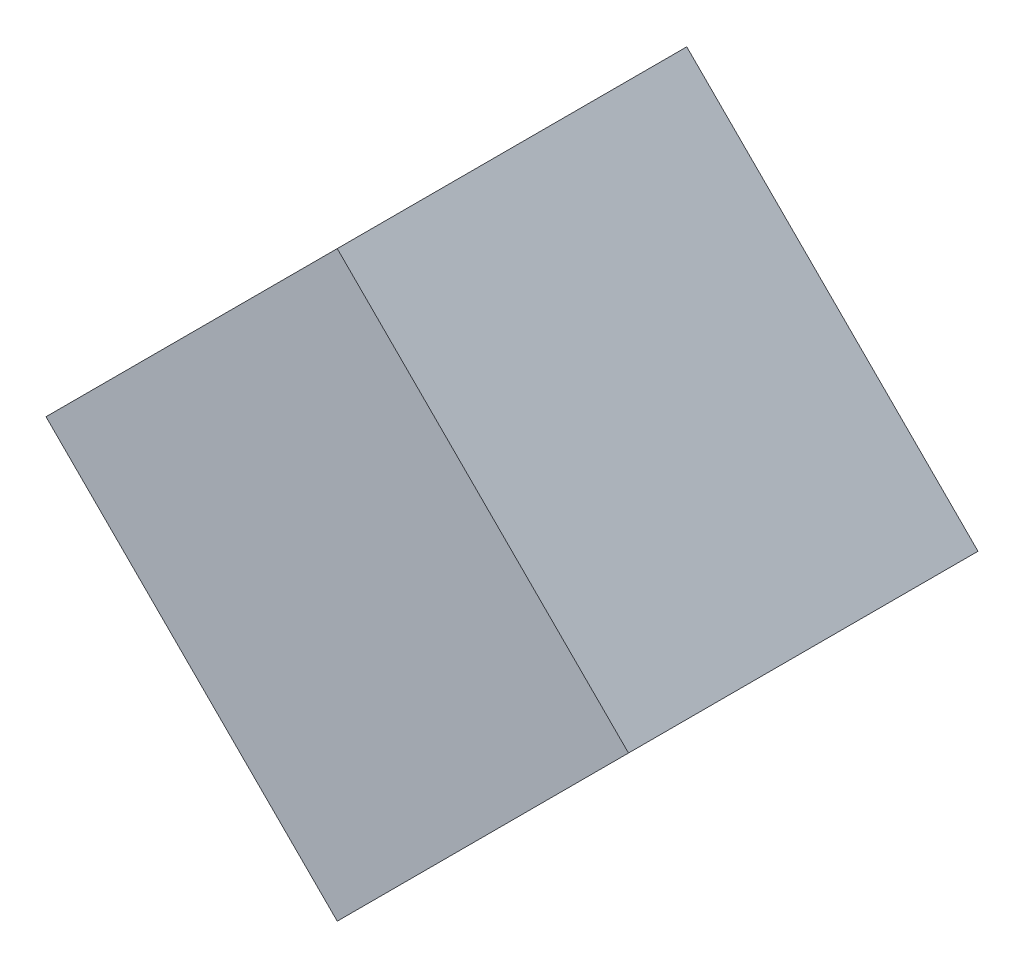
SolidWorks part; units mm, degrees
ref_plane "Piano frontale" through (0, 0, 0) normal (0, 0, 1) x (1, 0, 0)
ref_plane "Piano superiore" through (0, 0, 0) normal (0, 1, 0) x (1, 0, 0)
ref_plane "Piano destro" through (0, 0, 0) normal (1, 0, 0) x (0, 0, -1)
sketch "Schizzo1" plane through (0, 0, 0) normal (0, 0, 1) x (1, 0, 0)
  line L1 (25, 0) -> (0, 25)
  line L2 (0, 25) -> (-25, 0)
  line L3 (-25, 0) -> (0, -25)
  line L4 (0, -25) -> (25, 0)
  circle A0 centre (0, 0) radius 25 construction
extrude "Estrusione-Estrusione1" add sketch "Schizzo1" along normal blind 30
